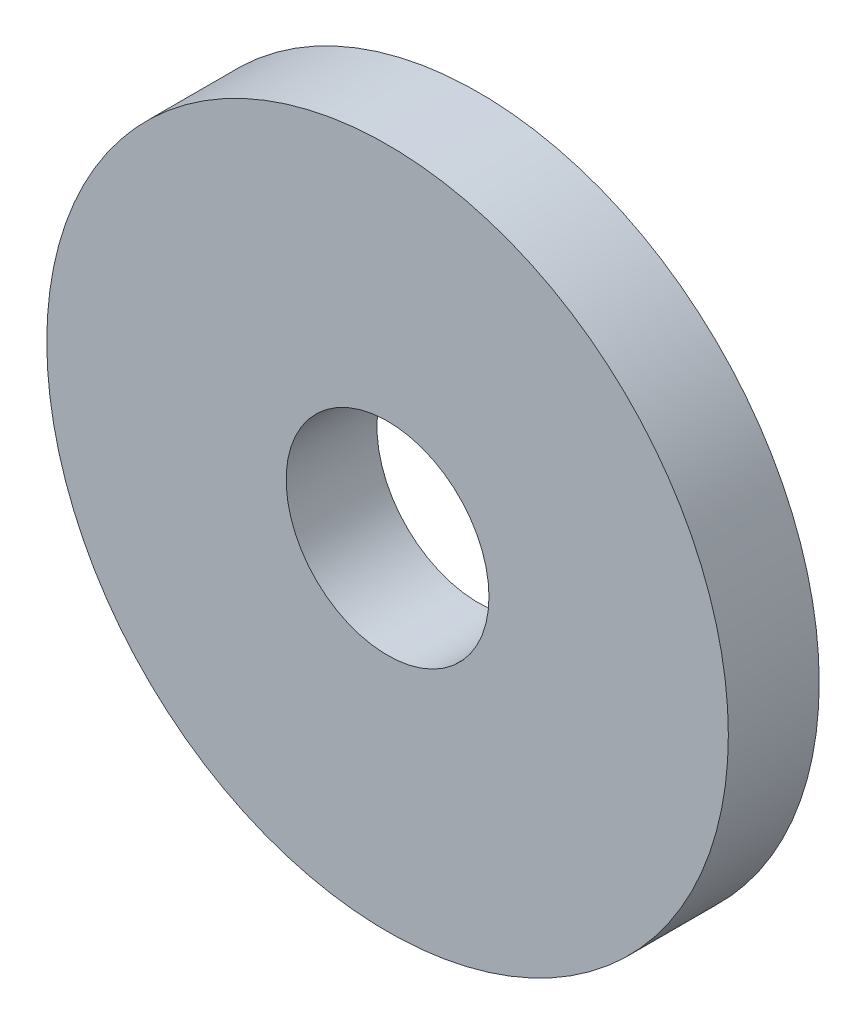
SolidWorks part; units mm, degrees
ref_plane "Front Plane" through (0, 0, 0) normal (0, 0, 1) x (1, 0, 0)
ref_plane "Top Plane" through (0, 0, 0) normal (0, 1, 0) x (1, 0, 0)
ref_plane "Right Plane" through (0, 0, 0) normal (1, 0, 0) x (0, 0, -1)
sketch "Sketch1" plane through (0, 0, 0) normal (0, 0, 1) x (1, 0, 0)
  circle A0 centre (0, 0) radius 16.002
  circle A2 centre (0, 0) radius 4.7625
  dimension "D1" = 32.004
  dimension "D2" = 9.525
extrude "Boss-Extrude1" add sketch "Sketch1" along normal mid plane 4.2672
